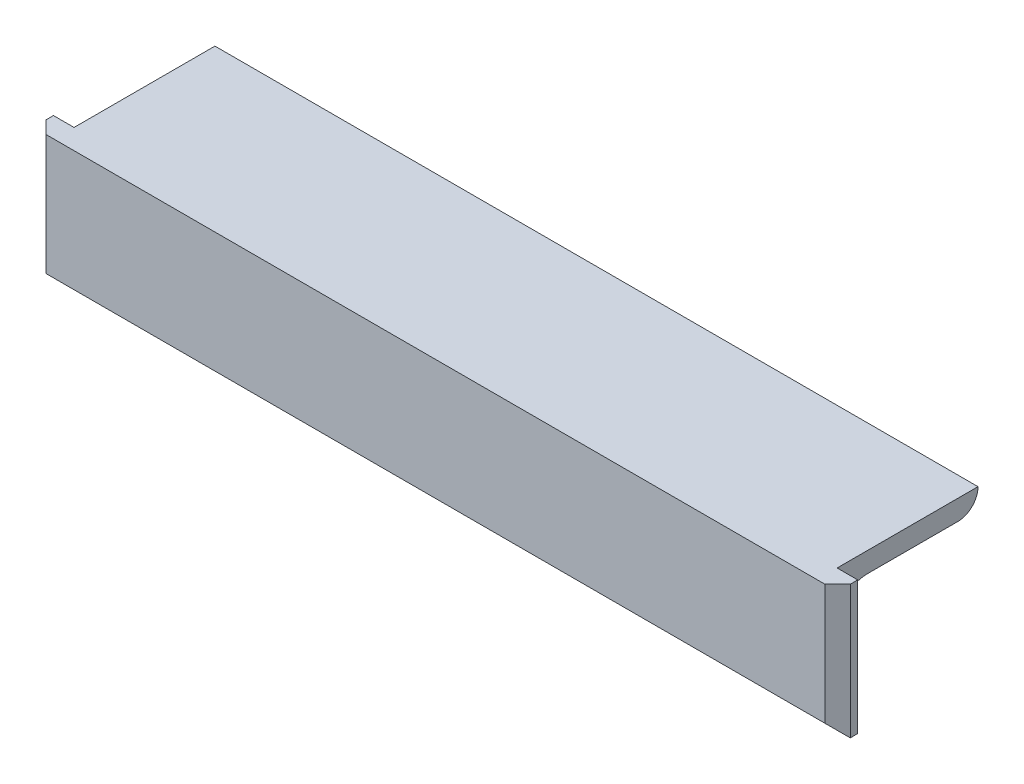
SolidWorks part; units mm, degrees
ref_plane "Alzado" through (0, 0, 0) normal (0, 0, 1) x (1, 0, 0)
ref_plane "Planta" through (0, 0, 0) normal (0, 1, 0) x (1, 0, 0)
ref_plane "Vista lateral" through (0, 0, 0) normal (1, 0, 0) x (0, 0, -1)
sketch "Croquis1" plane through (0, 0, 0) normal (0, 0, 1) x (1, 0, 0)
  line L0 (-63.435, 0) -> (63.435, 0)
  point P4 (0, 0)
  dimension "D1" = 126.87
other "Hierro angular 1 X 1 X 0.125(1)"
ref_plane "Plano1" through (-63.435, 0, 0) normal (1, 0, 0) x (0, -1, 0)
sketch "Sketch1" plane through (-63.435, 0, 0) normal (1, 0, 0) x (0, -1, 0)
  line L0 (0, 0) -> (0, 25.4)
  line L1 (0, 25.4) -> (0.0051, 25.4)
  line L2 (3.175, 22.2301) -> (3.175, 7.9375)
  line L3 (7.9375, 3.175) -> (22.2301, 3.175)
  line L4 (25.4, 0.0051) -> (25.4, 0)
  line L5 (25.4, 0) -> (0, 0)
  arc A0 (25.4, 0.0051) -> (22.2301, 3.175) centre (22.2301, 0.0051) ccw
  arc A1 (0.0051, 25.4) -> (3.175, 22.2301) centre (0.0051, 22.2301) cw
  arc A2 (7.9375, 3.175) -> (3.175, 7.9375) centre (7.9375, 7.9375) cw
  point P10 (12.7, 0)
  point P14 (0, 12.7)
  point P15 (3.175, 12.7)
  point P16 (12.7, 3.175)
  point P17 (3.175, 25.4)
  point P18 (25.4, 3.175)
  point P19 (0, 0)
  dimension "D2" = 0.0051
  dimension "Radius_1" = 4.7625
  dimension "D1" = 3.175
  dimension "H_leg" = 25.4
sketch "Croquis3" plane through (0, 0, 0) normal (0, 1, 0) x (1, 0, 0)
  line L0 (63.435, 3.175) -> (-63.435, 3.175) construction
  line L1 (63.435, 3.175) -> (-63.435, 3.175)
  line L2 (0, 3.175) -> (0, 25.4) construction
  line L3 (63.435, 25.4) -> (-63.435, 25.4) construction
  line L4 (-60.185, 25.4) -> (-60.185, 3.175)
  line L5 (-60.185, 25.4) -> (-63.435, 25.4)
  line L6 (-63.435, 25.4) -> (-63.435, 3.175)
  line L7 (60.185, 25.4) -> (63.435, 25.4)
  line L8 (63.435, 25.4) -> (63.435, 3.175)
  line L9 (60.185, 25.4) -> (60.185, 3.175)
  line M5 (-63.435, 25.4) -> (-63.435, 0)
  line M7 (63.435, 0) -> (63.435, 25.4)
  line M8 (63.435, 25.4) -> (-63.435, 25.4)
  dimension "D1" = 60.185
extrude "Cortar-Extruir1" cut sketch "Croquis3" against normal blind 10 contours L4 L1 M8 M5 | L9 L1 M8 M7
sketch "Croquis4" plane through (0, 0, 0) normal (0, 0, 1) x (1, 0, 0)
  line L0 (-63.435, -21) -> (63.435, -21)
  line L1 (-63.435, 0) -> (-63.435, -25.4) construction
  line L2 (63.435, 0) -> (63.435, -25.4) construction
  line L3 (-63.435, 0) -> (63.435, 0) construction
  line L4 (-63.435, -21) -> (-63.435, -25.4)
  line L5 (-63.435, -25.4) -> (63.435, -25.4)
  line L6 (63.435, -25.4) -> (63.435, -21)
  dimension "D1" = 21
extrude "Cortar-Extruir2" cut sketch "Croquis4" against normal blind 10
chamfer "Chaflán1" distance 2 angle 45 1 edges at (0, -21, 0)
chamfer "Chaflán2" distance 2 angle 45 2 edges at (63.435, -9.5, 0) (-63.435, -9.5, 0)
